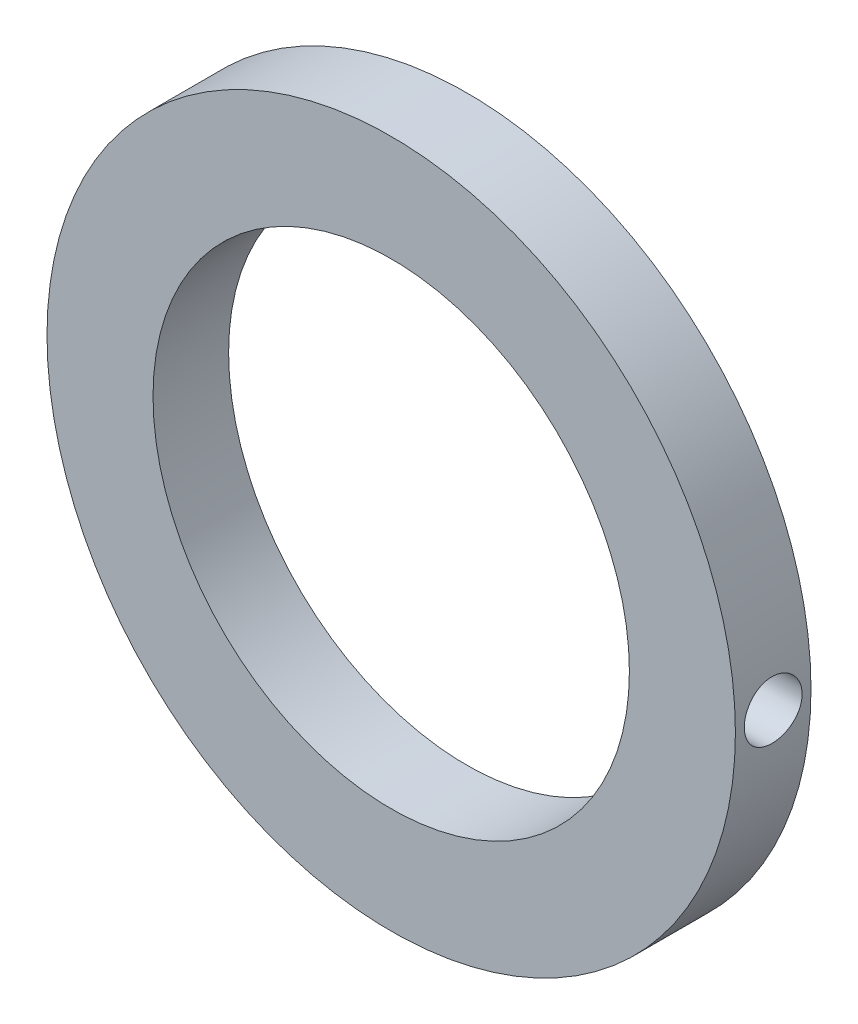
SolidWorks part; units mm, degrees
material "AISI 1020"
ref_plane "Plano frontal" through (0, 0, 0) normal (0, 0, 1) x (1, 0, 0)
ref_plane "Plano superior" through (0, 0, 0) normal (0, 1, 0) x (1, 0, 0)
ref_plane "Plano direito" through (0, 0, 0) normal (1, 0, 0) x (0, 0, -1)
sketch "Esboço1" plane through (0, 0, 0) normal (0, 0, 1) x (1, 0, 0)
  circle A0 centre (0, 0) radius 25
  circle A1 centre (0, 0) radius 17.3
  dimension "D1" = 50
  dimension "D2" = 34.6
extrude "Ressalto-extrusão1" add sketch "Esboço1" along normal blind 5.49
hole_wizard "Furo roscado de M5x0.81" positions "Esboço6" profile "Esboço2" tap size "M5x0.8" standard "Ansi Metric"
sketch "Esboço6" plane through (0, 0, 0) normal (1, 0, 0) x (0, 0, -1)
  point P0 (-2.745, 0)
sketch "Esboço2" plane through (0, 0, 2.745) normal (0, 1, 0) x (0, 0, 1)
  line L0 (0, 0) -> (0, 25)
  line L1 (0, 25) -> (2.1, 25)
  line L2 (2.1, 25) -> (2.1, 0)
  line L5 (2.1, 0) -> (0, 0)
  line L11 (0, -6.35) -> (0, 107.95) construction
  dimension "Thru Tap Drill Dia." = 4.2
  dimension "Thru Tap Drill Depth" = 25
cosmetic thread "Rosca de furo1" parameters "D2"=5
